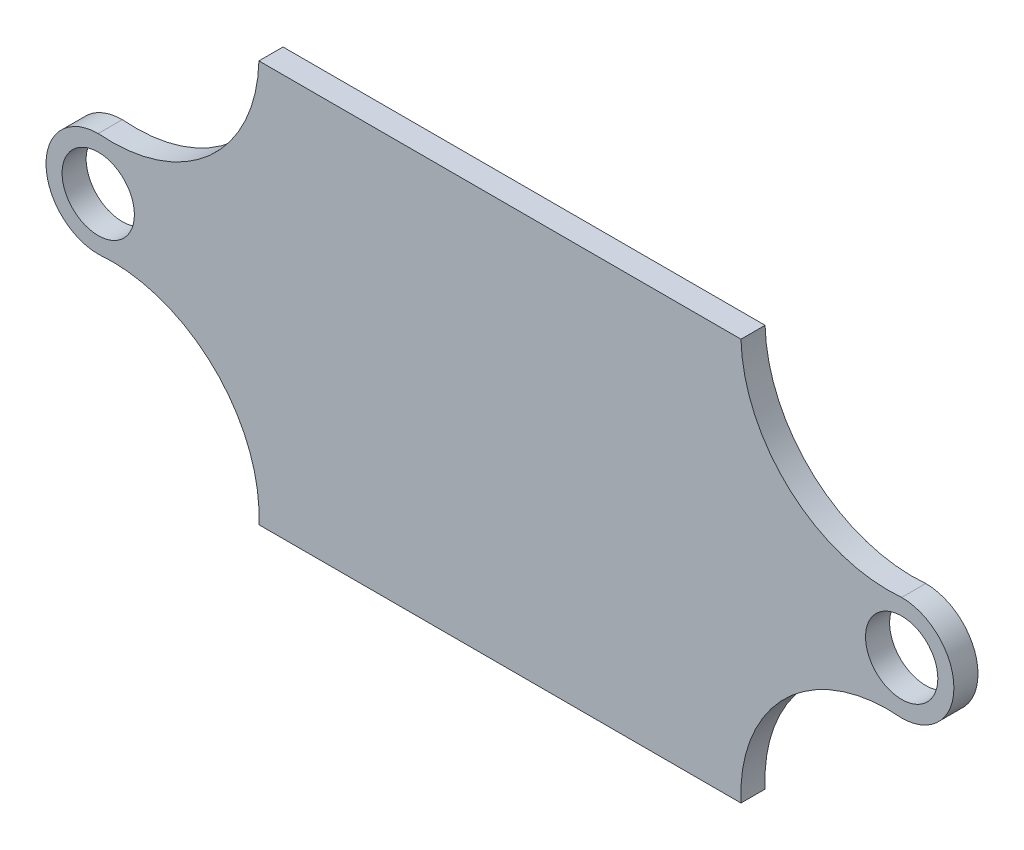
SolidWorks part; units mm, degrees
material "Cedar"
ref_plane "Front Plane" through (0, 0, 0) normal (0, 0, 1) x (1, 0, 0)
ref_plane "Top Plane" through (0, 0, 0) normal (0, 1, 0) x (1, 0, 0)
ref_plane "Right Plane" through (0, 0, 0) normal (1, 0, 0) x (0, 0, -1)
sketch "Sketch2" plane through (0, 0, 0) normal (0, 0, 1) x (1, 0, 0)
  line L0 (0, 15.2462) -> (0, -11.0795) construction
  line L1 (-30, -25) -> (30, -25)
  line L2 (-30, -25) -> (-30, -23.2039)
  line L3 (-30, 25) -> (30, 25)
  line L4 (30, -25) -> (30, -23.2039)
  line L5 (-30, -25) -> (30, 25) construction
  line L6 (-30, 25) -> (30, -25) construction
  arc A0 (50, -5.8345) -> (50, 7.1655) centre (50, 0.6655) ccw
  circle A1 centre (50, 0.6655) radius 4.5
  arc A2 (30, 25) -> (50, 7.1655) centre (48.3392, 25.4345) ccw
  arc A3 (30, -25) -> (50, -5.8345) centre (48.3223, -24.1019) cw
  arc A4 (-30, -25) -> (-50, -5.8345) centre (-48.3223, -24.1019) ccw
  arc A5 (-30, 25) -> (-50, 7.1655) centre (-48.3392, 25.4345) cw
  circle A6 centre (-50, 0.6655) radius 4.5
  arc A7 (-50, -5.8345) -> (-50, 7.1655) centre (-50, 0.6655) cw
  point P0 (0, 0)
  dimension "D3" = 13
  dimension "D4" = 9
  dimension "D1" = 60
  dimension "D2" = 50
  dimension "D5" = 20
  dimension "D6" = 20
extrude "Boss-Extrude2" add sketch "Sketch2" along normal blind 3 contours A7 A4 L1 A3 A0 A2 L3 A5 A1 A6
